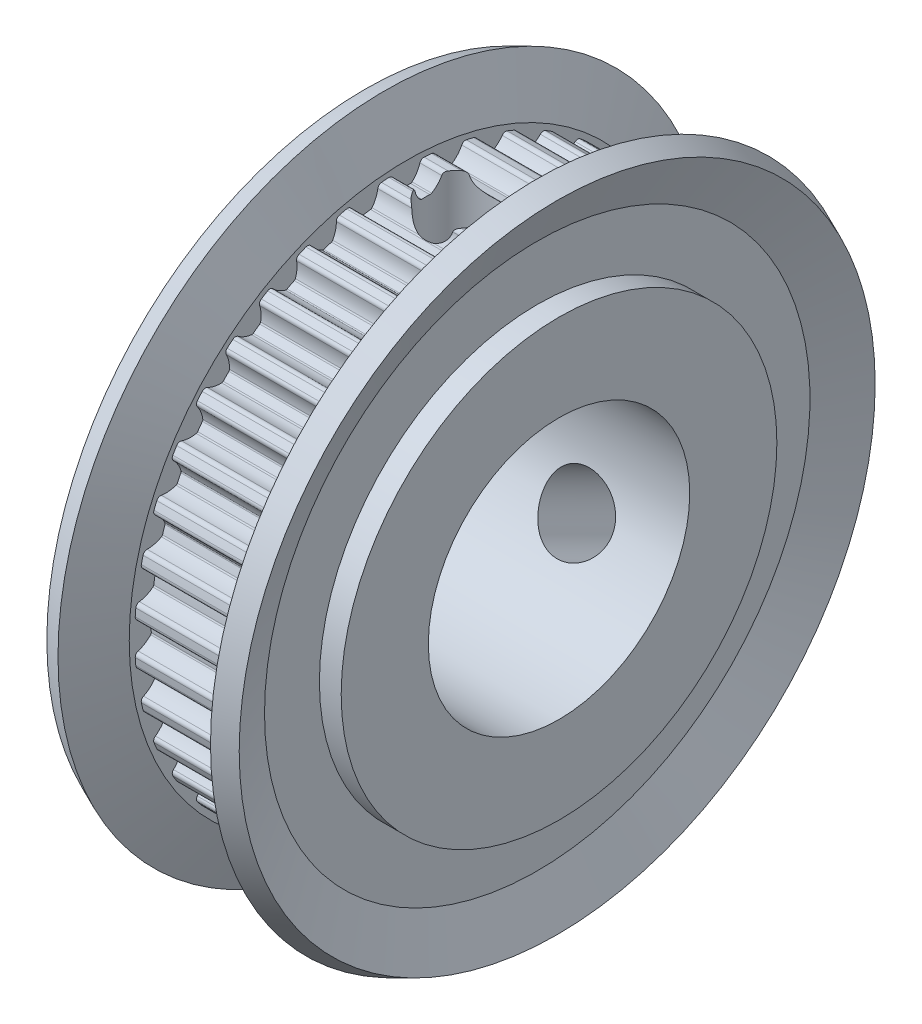
SolidWorks part; units mm, degrees
ref_plane "Front Plane" through (0, 0, 0) normal (0, 0, 1) x (1, 0, 0)
ref_plane "Top Plane" through (0, 0, 0) normal (0, 1, 0) x (1, 0, 0)
ref_plane "Right Plane" through (0, 0, 0) normal (1, 0, 0) x (0, 0, -1)
ref_plane "Plane1" through (0, 0, 0) normal (0, 0, 1) x (1, 0, 0)
sketch "Sketch1" plane through (0, 0, 0) normal (0, 0, 1) x (1, 0, 0)
  line L0 (0, 10) -> (0, 6)
  line L1 (0, 6) -> (17, 6)
  line L2 (17, 6) -> (17, 7)
  line L3 (17, 7) -> (9, 7)
  line L4 (9, 7) -> (9, 10)
  line L5 (9, 10) -> (8, 10)
  line L6 (8, 10) -> (8, 12.5195)
  line L7 (8, 12.5195) -> (8.9151, 14.5969)
  line L8 (8.9151, 14.5969) -> (8, 15)
  line L9 (8, 15) -> (7, 12.73)
  line L10 (7, 12.73) -> (7, 12.48)
  line L11 (7, 12.48) -> (2, 12.48)
  line L12 (2, 12.48) -> (2, 12.73)
  line L13 (2, 12.73) -> (1, 15)
  line L14 (1, 15) -> (0.0849, 14.5969)
  line L15 (0.0849, 14.5969) -> (1, 12.5195)
  line L16 (1, 12.5195) -> (1, 10)
  line L17 (1, 10) -> (0, 10)
  line L18 (17, 0) -> (0, 0) construction
revolve "Revolve1" add sketch "Sketch1" angle 360 about L18
ref_plane "Plane2" through (0, 0, 0) normal (0, 0, 1) x (1, 0, 0)
sketch "Sketch2" plane through (0, 0, 0) normal (0, 0, 1) x (1, 0, 0)
  line L0 (9, 0) -> (9, 15)
  line L1 (9, 15) -> (18, 15)
  line L2 (18, 15) -> (18, 0)
  line L3 (18, 0) -> (9, 0)
  line L4 (18, 0) -> (9, 0) construction
revolve "Cut-Revolve1" cut sketch "Sketch2" angle 360 about L4
ref_plane "Plane3" through (2, 0, 0) normal (1, 0, 0) x (0, 0, -1)
sketch "Sketch3" plane through (2, 0, 0) normal (1, 0, 0) x (0, 0, -1)
  line L0 (0.8092, 12.4537) -> (0.8092, 16.64)
  line L1 (0.8092, 16.64) -> (-0.8092, 16.64)
  line L2 (-0.8092, 16.64) -> (-0.8092, 12.4537)
  arc A0 (-0.8092, 12.4537) -> (-0.6154, 12.3205) centre (-0.7969, 12.2641) cw
  arc A1 (-0.6154, 12.3205) -> (-0.2549, 11.7455) centre (0.65, 12.7134) ccw
  arc A2 (-0.2549, 11.7455) -> (-0.185, 11.7185) centre (-0.1866, 11.8185) ccw
  arc A3 (-0.185, 11.7185) -> (0.185, 11.7185) centre (0, 0) cw
  arc A4 (0.185, 11.7185) -> (0.2549, 11.7455) centre (0.1866, 11.8185) ccw
  arc A5 (0.2549, 11.7455) -> (0.6154, 12.3205) centre (-0.65, 12.7134) ccw
  arc A6 (0.6154, 12.3205) -> (0.8092, 12.4537) centre (0.7969, 12.2641) cw
extrude "Cut-Extrude1" cut sketch "Sketch3" along normal blind 5
ref_plane "Plane4" through (2, 0, 0) normal (1, 0, 0) x (0, 0, -1)
sketch "Sketch4" plane through (2, 0, 0) normal (1, 0, 0) x (0, 0, -1)
  line L0 (-1.149, 12.427) -> (-1.8039, 16.5617)
  line L1 (-1.8039, 16.5617) -> (-3.4023, 16.3086)
  line L2 (-3.4023, 16.3086) -> (-2.7474, 12.1738)
  arc A0 (-2.7474, 12.1738) -> (-2.5352, 12.0725) centre (-2.7056, 11.9885) cw
  arc A1 (-2.5352, 12.0725) -> (-2.0891, 11.561) centre (-1.3468, 12.6586) ccw
  arc A2 (-2.0891, 11.561) -> (-2.0159, 11.5453) centre (-2.0331, 11.6438) ccw
  arc A3 (-2.0159, 11.5453) -> (-1.6505, 11.6032) centre (0, 0) cw
  arc A4 (-1.6505, 11.6032) -> (-1.5857, 11.6407) centre (-1.6646, 11.7022) ccw
  arc A5 (-1.5857, 11.6407) -> (-1.3195, 12.2651) centre (-2.6308, 12.4552) ccw
  arc A6 (-1.3195, 12.2651) -> (-1.149, 12.427) centre (-1.1315, 12.2378) cw
extrude "Cut-Extrude2" cut sketch "Sketch4" along normal blind 5
ref_plane "Plane5" through (2, 0, 0) normal (1, 0, 0) x (0, 0, -1)
sketch "Sketch5" plane through (2, 0, 0) normal (1, 0, 0) x (0, 0, -1)
  line L0 (-3.0788, 12.0943) -> (-4.3725, 16.0756)
  line L1 (-4.3725, 16.0756) -> (-5.9116, 15.5755)
  line L2 (-5.9116, 15.5755) -> (-4.618, 11.5942)
  arc A0 (-4.618, 11.5942) -> (-4.3925, 11.5273) centre (-4.5477, 11.4176) cw
  arc A1 (-4.3925, 11.5273) -> (-3.8719, 11.0919) centre (-3.3105, 12.292) ccw
  arc A2 (-3.8719, 11.0919) -> (-3.7972, 11.0878) centre (-3.8296, 11.1824) ccw
  arc A3 (-3.7972, 11.0878) -> (-3.4453, 11.2022) centre (0, 0) cw
  arc A4 (-3.4453, 11.2022) -> (-3.3872, 11.2494) centre (-3.4747, 11.2977) ccw
  arc A5 (-3.3872, 11.2494) -> (-3.222, 11.9076) centre (-4.5468, 11.8903) ccw
  arc A6 (-3.222, 11.9076) -> (-3.0788, 12.0943) centre (-3.032, 11.9101) cw
extrude "Cut-Extrude3" cut sketch "Sketch5" along normal blind 5
ref_plane "Plane6" through (2, 0, 0) normal (1, 0, 0) x (0, 0, -1)
sketch "Sketch6" plane through (2, 0, 0) normal (1, 0, 0) x (0, 0, -1)
  line L0 (-4.9329, 11.4637) -> (-6.8334, 15.1937)
  line L1 (-6.8334, 15.1937) -> (-8.2754, 14.459)
  line L2 (-8.2754, 14.459) -> (-6.3749, 10.729)
  arc A0 (-6.3749, 10.729) -> (-6.1417, 10.6982) centre (-6.2778, 10.5657) cw
  arc A1 (-6.1417, 10.6982) -> (-5.5594, 10.3496) centre (-5.1926, 11.6228) ccw
  arc A2 (-5.5594, 10.3496) -> (-5.4849, 10.3573) centre (-5.5317, 10.4457) ccw
  arc A3 (-5.4849, 10.3573) -> (-5.1553, 10.5253) centre (0, 0) cw
  arc A4 (-5.1553, 10.5253) -> (-5.1053, 10.581) centre (-5.1993, 10.6151) ccw
  arc A5 (-5.1053, 10.581) -> (-5.0451, 11.257) centre (-6.3509, 11.0326) ccw
  arc A6 (-5.0451, 11.257) -> (-4.9329, 11.4637) centre (-4.8578, 11.2892) cw
extrude "Cut-Extrude4" cut sketch "Sketch6" along normal blind 5
ref_plane "Plane7" through (2, 0, 0) normal (1, 0, 0) x (0, 0, -1)
sketch "Sketch7" plane through (2, 0, 0) normal (1, 0, 0) x (0, 0, -1)
  line L0 (-6.6655, 10.5509) -> (-9.1261, 13.9377)
  line L1 (-9.1261, 13.9377) -> (-10.4354, 12.9864)
  line L2 (-10.4354, 12.9864) -> (-7.9748, 9.5997)
  arc A0 (-7.9748, 9.5997) -> (-7.7397, 9.6058) centre (-7.8534, 9.4535) cw
  arc A1 (-7.7397, 9.6058) -> (-7.11, 9.3525) centre (-6.9469, 10.6674) ccw
  arc A2 (-7.11, 9.3525) -> (-7.0376, 9.3718) centre (-7.0977, 9.4517) ccw
  arc A3 (-7.0376, 9.3718) -> (-6.7383, 9.5892) centre (0, 0) cw
  arc A4 (-6.7383, 9.5892) -> (-6.6976, 9.6521) centre (-6.7958, 9.671) ccw
  arc A5 (-6.6976, 9.6521) -> (-6.7439, 10.3292) centre (-7.9986, 9.9033) ccw
  arc A6 (-6.7439, 10.3292) -> (-6.6655, 10.5509) centre (-6.564, 10.3903) cw
extrude "Cut-Extrude5" cut sketch "Sketch7" along normal blind 5
ref_plane "Plane8" through (2, 0, 0) normal (1, 0, 0) x (0, 0, -1)
sketch "Sketch8" plane through (2, 0, 0) normal (1, 0, 0) x (0, 0, -1)
  line L0 (-8.2339, 9.3783) -> (-11.1941, 12.3384)
  line L1 (-11.1941, 12.3384) -> (-12.3384, 11.1941)
  line L2 (-12.3384, 11.1941) -> (-9.3783, 8.2339)
  arc A0 (-9.3783, 8.2339) -> (-9.1471, 8.2767) centre (-9.2355, 8.1086) cw
  arc A1 (-9.1471, 8.2767) -> (-8.4855, 8.1251) centre (-8.5301, 9.4493) ccw
  arc A2 (-8.4855, 8.1251) -> (-8.4171, 8.1555) centre (-8.4889, 8.225) ccw
  arc A3 (-8.4171, 8.1555) -> (-8.1555, 8.4171) centre (0, 0) cw
  arc A4 (-8.1555, 8.4171) -> (-8.1251, 8.4855) centre (-8.225, 8.4889) ccw
  arc A5 (-8.1251, 8.4855) -> (-8.2767, 9.1471) centre (-9.4493, 8.5301) ccw
  arc A6 (-8.2767, 9.1471) -> (-8.2339, 9.3783) centre (-8.1086, 9.2355) cw
extrude "Cut-Extrude6" cut sketch "Sketch8" along normal blind 5
ref_plane "Plane9" through (2, 0, 0) normal (1, 0, 0) x (0, 0, -1)
sketch "Sketch9" plane through (2, 0, 0) normal (1, 0, 0) x (0, 0, -1)
  line L0 (-9.5997, 7.9748) -> (-12.9864, 10.4354)
  line L1 (-12.9864, 10.4354) -> (-13.9377, 9.1261)
  line L2 (-13.9377, 9.1261) -> (-10.5509, 6.6655)
  arc A0 (-10.5509, 6.6655) -> (-10.3292, 6.7439) centre (-10.3903, 6.564) cw
  arc A1 (-10.3292, 6.7439) -> (-9.6521, 6.6976) centre (-9.9033, 7.9986) ccw
  arc A2 (-9.6521, 6.6976) -> (-9.5892, 6.7383) centre (-9.671, 6.7958) ccw
  arc A3 (-9.5892, 6.7383) -> (-9.3718, 7.0376) centre (0, 0) cw
  arc A4 (-9.3718, 7.0376) -> (-9.3525, 7.11) centre (-9.4517, 7.0977) ccw
  arc A5 (-9.3525, 7.11) -> (-9.6058, 7.7397) centre (-10.6674, 6.9469) ccw
  arc A6 (-9.6058, 7.7397) -> (-9.5997, 7.9748) centre (-9.4535, 7.8534) cw
extrude "Cut-Extrude7" cut sketch "Sketch9" along normal blind 5
ref_plane "Plane10" through (2, 0, 0) normal (1, 0, 0) x (0, 0, -1)
sketch "Sketch10" plane through (2, 0, 0) normal (1, 0, 0) x (0, 0, -1)
  line L0 (-10.729, 6.3749) -> (-14.459, 8.2754)
  line L1 (-14.459, 8.2754) -> (-15.1937, 6.8334)
  line L2 (-15.1937, 6.8334) -> (-11.4637, 4.9329)
  arc A0 (-11.4637, 4.9329) -> (-11.257, 5.0451) centre (-11.2892, 4.8578) cw
  arc A1 (-11.257, 5.0451) -> (-10.581, 5.1053) centre (-11.0326, 6.3509) ccw
  arc A2 (-10.581, 5.1053) -> (-10.5253, 5.1553) centre (-10.6151, 5.1993) ccw
  arc A3 (-10.5253, 5.1553) -> (-10.3573, 5.4849) centre (0, 0) cw
  arc A4 (-10.3573, 5.4849) -> (-10.3496, 5.5594) centre (-10.4457, 5.5317) ccw
  arc A5 (-10.3496, 5.5594) -> (-10.6982, 6.1417) centre (-11.6228, 5.1926) ccw
  arc A6 (-10.6982, 6.1417) -> (-10.729, 6.3749) centre (-10.5657, 6.2778) cw
extrude "Cut-Extrude8" cut sketch "Sketch10" along normal blind 5
ref_plane "Plane11" through (2, 0, 0) normal (1, 0, 0) x (0, 0, -1)
sketch "Sketch11" plane through (2, 0, 0) normal (1, 0, 0) x (0, 0, -1)
  line L0 (-11.5942, 4.618) -> (-15.5755, 5.9116)
  line L1 (-15.5755, 5.9116) -> (-16.0756, 4.3725)
  line L2 (-16.0756, 4.3725) -> (-12.0943, 3.0788)
  arc A0 (-12.0943, 3.0788) -> (-11.9076, 3.222) centre (-11.9101, 3.032) cw
  arc A1 (-11.9076, 3.222) -> (-11.2494, 3.3872) centre (-11.8903, 4.5468) ccw
  arc A2 (-11.2494, 3.3872) -> (-11.2022, 3.4453) centre (-11.2977, 3.4747) ccw
  arc A3 (-11.2022, 3.4453) -> (-11.0878, 3.7972) centre (0, 0) cw
  arc A4 (-11.0878, 3.7972) -> (-11.0919, 3.8719) centre (-11.1824, 3.8296) ccw
  arc A5 (-11.0919, 3.8719) -> (-11.5273, 4.3925) centre (-12.292, 3.3105) ccw
  arc A6 (-11.5273, 4.3925) -> (-11.5942, 4.618) centre (-11.4176, 4.5477) cw
extrude "Cut-Extrude9" cut sketch "Sketch11" along normal blind 5
ref_plane "Plane12" through (2, 0, 0) normal (1, 0, 0) x (0, 0, -1)
sketch "Sketch12" plane through (2, 0, 0) normal (1, 0, 0) x (0, 0, -1)
  line L0 (-12.1738, 2.7474) -> (-16.3086, 3.4023)
  line L1 (-16.3086, 3.4023) -> (-16.5617, 1.8039)
  line L2 (-16.5617, 1.8039) -> (-12.427, 1.149)
  arc A0 (-12.427, 1.149) -> (-12.2651, 1.3195) centre (-12.2378, 1.1315) cw
  arc A1 (-12.2651, 1.3195) -> (-11.6407, 1.5857) centre (-12.4552, 2.6308) ccw
  arc A2 (-11.6407, 1.5857) -> (-11.6032, 1.6505) centre (-11.7022, 1.6646) ccw
  arc A3 (-11.6032, 1.6505) -> (-11.5453, 2.0159) centre (0, 0) cw
  arc A4 (-11.5453, 2.0159) -> (-11.561, 2.0891) centre (-11.6438, 2.0331) ccw
  arc A5 (-11.561, 2.0891) -> (-12.0725, 2.5352) centre (-12.6586, 1.3468) ccw
  arc A6 (-12.0725, 2.5352) -> (-12.1738, 2.7474) centre (-11.9885, 2.7056) cw
extrude "Cut-Extrude10" cut sketch "Sketch12" along normal blind 5
ref_plane "Plane13" through (2, 0, 0) normal (1, 0, 0) x (0, 0, -1)
sketch "Sketch13" plane through (2, 0, 0) normal (1, 0, 0) x (0, 0, -1)
  line L0 (-12.4537, 0.8092) -> (-16.64, 0.8092)
  line L1 (-16.64, 0.8092) -> (-16.64, -0.8092)
  line L2 (-16.64, -0.8092) -> (-12.4537, -0.8092)
  arc A0 (-12.4537, -0.8092) -> (-12.3205, -0.6154) centre (-12.2641, -0.7969) cw
  arc A1 (-12.3205, -0.6154) -> (-11.7455, -0.2549) centre (-12.7134, 0.65) ccw
  arc A2 (-11.7455, -0.2549) -> (-11.7185, -0.185) centre (-11.8185, -0.1866) ccw
  arc A3 (-11.7185, -0.185) -> (-11.7185, 0.185) centre (0, 0) cw
  arc A4 (-11.7185, 0.185) -> (-11.7455, 0.2549) centre (-11.8185, 0.1866) ccw
  arc A5 (-11.7455, 0.2549) -> (-12.3205, 0.6154) centre (-12.7134, -0.65) ccw
  arc A6 (-12.3205, 0.6154) -> (-12.4537, 0.8092) centre (-12.2641, 0.7969) cw
extrude "Cut-Extrude11" cut sketch "Sketch13" along normal blind 5
ref_plane "Plane14" through (2, 0, 0) normal (1, 0, 0) x (0, 0, -1)
sketch "Sketch14" plane through (2, 0, 0) normal (1, 0, 0) x (0, 0, -1)
  line L0 (-12.427, -1.149) -> (-16.5617, -1.8039)
  line L1 (-16.5617, -1.8039) -> (-16.3086, -3.4023)
  line L2 (-16.3086, -3.4023) -> (-12.1738, -2.7474)
  arc A0 (-12.1738, -2.7474) -> (-12.0725, -2.5352) centre (-11.9885, -2.7056) cw
  arc A1 (-12.0725, -2.5352) -> (-11.561, -2.0891) centre (-12.6586, -1.3468) ccw
  arc A2 (-11.561, -2.0891) -> (-11.5453, -2.0159) centre (-11.6438, -2.0331) ccw
  arc A3 (-11.5453, -2.0159) -> (-11.6032, -1.6505) centre (0, 0) cw
  arc A4 (-11.6032, -1.6505) -> (-11.6407, -1.5857) centre (-11.7022, -1.6646) ccw
  arc A5 (-11.6407, -1.5857) -> (-12.2651, -1.3195) centre (-12.4552, -2.6308) ccw
  arc A6 (-12.2651, -1.3195) -> (-12.427, -1.149) centre (-12.2378, -1.1315) cw
extrude "Cut-Extrude12" cut sketch "Sketch14" along normal blind 5
ref_plane "Plane15" through (2, 0, 0) normal (1, 0, 0) x (0, 0, -1)
sketch "Sketch15" plane through (2, 0, 0) normal (1, 0, 0) x (0, 0, -1)
  line L0 (-12.0943, -3.0788) -> (-16.0756, -4.3725)
  line L1 (-16.0756, -4.3725) -> (-15.5755, -5.9116)
  line L2 (-15.5755, -5.9116) -> (-11.5942, -4.618)
  arc A0 (-11.5942, -4.618) -> (-11.5273, -4.3925) centre (-11.4176, -4.5477) cw
  arc A1 (-11.5273, -4.3925) -> (-11.0919, -3.8719) centre (-12.292, -3.3105) ccw
  arc A2 (-11.0919, -3.8719) -> (-11.0878, -3.7972) centre (-11.1824, -3.8296) ccw
  arc A3 (-11.0878, -3.7972) -> (-11.2022, -3.4453) centre (0, 0) cw
  arc A4 (-11.2022, -3.4453) -> (-11.2494, -3.3872) centre (-11.2977, -3.4747) ccw
  arc A5 (-11.2494, -3.3872) -> (-11.9076, -3.222) centre (-11.8903, -4.5468) ccw
  arc A6 (-11.9076, -3.222) -> (-12.0943, -3.0788) centre (-11.9101, -3.032) cw
extrude "Cut-Extrude13" cut sketch "Sketch15" along normal blind 5
ref_plane "Plane16" through (2, 0, 0) normal (1, 0, 0) x (0, 0, -1)
sketch "Sketch16" plane through (2, 0, 0) normal (1, 0, 0) x (0, 0, -1)
  line L0 (-11.4637, -4.9329) -> (-15.1937, -6.8334)
  line L1 (-15.1937, -6.8334) -> (-14.459, -8.2754)
  line L2 (-14.459, -8.2754) -> (-10.729, -6.3749)
  arc A0 (-10.729, -6.3749) -> (-10.6982, -6.1417) centre (-10.5657, -6.2778) cw
  arc A1 (-10.6982, -6.1417) -> (-10.3496, -5.5594) centre (-11.6228, -5.1926) ccw
  arc A2 (-10.3496, -5.5594) -> (-10.3573, -5.4849) centre (-10.4457, -5.5317) ccw
  arc A3 (-10.3573, -5.4849) -> (-10.5253, -5.1553) centre (0, 0) cw
  arc A4 (-10.5253, -5.1553) -> (-10.581, -5.1053) centre (-10.6151, -5.1993) ccw
  arc A5 (-10.581, -5.1053) -> (-11.257, -5.0451) centre (-11.0326, -6.3509) ccw
  arc A6 (-11.257, -5.0451) -> (-11.4637, -4.9329) centre (-11.2892, -4.8578) cw
extrude "Cut-Extrude14" cut sketch "Sketch16" along normal blind 5
ref_plane "Plane17" through (2, 0, 0) normal (1, 0, 0) x (0, 0, -1)
sketch "Sketch17" plane through (2, 0, 0) normal (1, 0, 0) x (0, 0, -1)
  line L0 (-10.5509, -6.6655) -> (-13.9377, -9.1261)
  line L1 (-13.9377, -9.1261) -> (-12.9864, -10.4354)
  line L2 (-12.9864, -10.4354) -> (-9.5997, -7.9748)
  arc A0 (-9.5997, -7.9748) -> (-9.6058, -7.7397) centre (-9.4535, -7.8534) cw
  arc A1 (-9.6058, -7.7397) -> (-9.3525, -7.11) centre (-10.6674, -6.9469) ccw
  arc A2 (-9.3525, -7.11) -> (-9.3718, -7.0376) centre (-9.4517, -7.0977) ccw
  arc A3 (-9.3718, -7.0376) -> (-9.5892, -6.7383) centre (0, 0) cw
  arc A4 (-9.5892, -6.7383) -> (-9.6521, -6.6976) centre (-9.671, -6.7958) ccw
  arc A5 (-9.6521, -6.6976) -> (-10.3292, -6.7439) centre (-9.9033, -7.9986) ccw
  arc A6 (-10.3292, -6.7439) -> (-10.5509, -6.6655) centre (-10.3903, -6.564) cw
extrude "Cut-Extrude15" cut sketch "Sketch17" along normal blind 5
ref_plane "Plane18" through (2, 0, 0) normal (1, 0, 0) x (0, 0, -1)
sketch "Sketch18" plane through (2, 0, 0) normal (1, 0, 0) x (0, 0, -1)
  line L0 (-9.3783, -8.2339) -> (-12.3384, -11.1941)
  line L1 (-12.3384, -11.1941) -> (-11.1941, -12.3384)
  line L2 (-11.1941, -12.3384) -> (-8.2339, -9.3783)
  arc A0 (-8.2339, -9.3783) -> (-8.2767, -9.1471) centre (-8.1086, -9.2355) cw
  arc A1 (-8.2767, -9.1471) -> (-8.1251, -8.4855) centre (-9.4493, -8.5301) ccw
  arc A2 (-8.1251, -8.4855) -> (-8.1555, -8.4171) centre (-8.225, -8.4889) ccw
  arc A3 (-8.1555, -8.4171) -> (-8.4171, -8.1555) centre (0, 0) cw
  arc A4 (-8.4171, -8.1555) -> (-8.4855, -8.1251) centre (-8.4889, -8.225) ccw
  arc A5 (-8.4855, -8.1251) -> (-9.1471, -8.2767) centre (-8.5301, -9.4493) ccw
  arc A6 (-9.1471, -8.2767) -> (-9.3783, -8.2339) centre (-9.2355, -8.1086) cw
extrude "Cut-Extrude16" cut sketch "Sketch18" along normal blind 5
ref_plane "Plane19" through (2, 0, 0) normal (1, 0, 0) x (0, 0, -1)
sketch "Sketch19" plane through (2, 0, 0) normal (1, 0, 0) x (0, 0, -1)
  line L0 (-7.9748, -9.5997) -> (-10.4354, -12.9864)
  line L1 (-10.4354, -12.9864) -> (-9.1261, -13.9377)
  line L2 (-9.1261, -13.9377) -> (-6.6655, -10.5509)
  arc A0 (-6.6655, -10.5509) -> (-6.7439, -10.3292) centre (-6.564, -10.3903) cw
  arc A1 (-6.7439, -10.3292) -> (-6.6976, -9.6521) centre (-7.9986, -9.9033) ccw
  arc A2 (-6.6976, -9.6521) -> (-6.7383, -9.5892) centre (-6.7958, -9.671) ccw
  arc A3 (-6.7383, -9.5892) -> (-7.0376, -9.3718) centre (0, 0) cw
  arc A4 (-7.0376, -9.3718) -> (-7.11, -9.3525) centre (-7.0977, -9.4517) ccw
  arc A5 (-7.11, -9.3525) -> (-7.7397, -9.6058) centre (-6.9469, -10.6674) ccw
  arc A6 (-7.7397, -9.6058) -> (-7.9748, -9.5997) centre (-7.8534, -9.4535) cw
extrude "Cut-Extrude17" cut sketch "Sketch19" along normal blind 5
ref_plane "Plane20" through (2, 0, 0) normal (1, 0, 0) x (0, 0, -1)
sketch "Sketch20" plane through (2, 0, 0) normal (1, 0, 0) x (0, 0, -1)
  line L0 (-6.3749, -10.729) -> (-8.2754, -14.459)
  line L1 (-8.2754, -14.459) -> (-6.8334, -15.1937)
  line L2 (-6.8334, -15.1937) -> (-4.9329, -11.4637)
  arc A0 (-4.9329, -11.4637) -> (-5.0451, -11.257) centre (-4.8578, -11.2892) cw
  arc A1 (-5.0451, -11.257) -> (-5.1053, -10.581) centre (-6.3509, -11.0326) ccw
  arc A2 (-5.1053, -10.581) -> (-5.1553, -10.5253) centre (-5.1993, -10.6151) ccw
  arc A3 (-5.1553, -10.5253) -> (-5.4849, -10.3573) centre (0, 0) cw
  arc A4 (-5.4849, -10.3573) -> (-5.5594, -10.3496) centre (-5.5317, -10.4457) ccw
  arc A5 (-5.5594, -10.3496) -> (-6.1417, -10.6982) centre (-5.1926, -11.6228) ccw
  arc A6 (-6.1417, -10.6982) -> (-6.3749, -10.729) centre (-6.2778, -10.5657) cw
extrude "Cut-Extrude18" cut sketch "Sketch20" along normal blind 5
ref_plane "Plane21" through (2, 0, 0) normal (1, 0, 0) x (0, 0, -1)
sketch "Sketch21" plane through (2, 0, 0) normal (1, 0, 0) x (0, 0, -1)
  line L0 (-4.618, -11.5942) -> (-5.9116, -15.5755)
  line L1 (-5.9116, -15.5755) -> (-4.3725, -16.0756)
  line L2 (-4.3725, -16.0756) -> (-3.0788, -12.0943)
  arc A0 (-3.0788, -12.0943) -> (-3.222, -11.9076) centre (-3.032, -11.9101) cw
  arc A1 (-3.222, -11.9076) -> (-3.3872, -11.2494) centre (-4.5468, -11.8903) ccw
  arc A2 (-3.3872, -11.2494) -> (-3.4453, -11.2022) centre (-3.4747, -11.2977) ccw
  arc A3 (-3.4453, -11.2022) -> (-3.7972, -11.0878) centre (0, 0) cw
  arc A4 (-3.7972, -11.0878) -> (-3.8719, -11.0919) centre (-3.8296, -11.1824) ccw
  arc A5 (-3.8719, -11.0919) -> (-4.3925, -11.5273) centre (-3.3105, -12.292) ccw
  arc A6 (-4.3925, -11.5273) -> (-4.618, -11.5942) centre (-4.5477, -11.4176) cw
extrude "Cut-Extrude19" cut sketch "Sketch21" along normal blind 5
ref_plane "Plane22" through (2, 0, 0) normal (1, 0, 0) x (0, 0, -1)
sketch "Sketch22" plane through (2, 0, 0) normal (1, 0, 0) x (0, 0, -1)
  line L0 (-2.7474, -12.1738) -> (-3.4023, -16.3086)
  line L1 (-3.4023, -16.3086) -> (-1.8039, -16.5617)
  line L2 (-1.8039, -16.5617) -> (-1.149, -12.427)
  arc A0 (-1.149, -12.427) -> (-1.3195, -12.2651) centre (-1.1315, -12.2378) cw
  arc A1 (-1.3195, -12.2651) -> (-1.5857, -11.6407) centre (-2.6308, -12.4552) ccw
  arc A2 (-1.5857, -11.6407) -> (-1.6505, -11.6032) centre (-1.6646, -11.7022) ccw
  arc A3 (-1.6505, -11.6032) -> (-2.0159, -11.5453) centre (0, 0) cw
  arc A4 (-2.0159, -11.5453) -> (-2.0891, -11.561) centre (-2.0331, -11.6438) ccw
  arc A5 (-2.0891, -11.561) -> (-2.5352, -12.0725) centre (-1.3468, -12.6586) ccw
  arc A6 (-2.5352, -12.0725) -> (-2.7474, -12.1738) centre (-2.7056, -11.9885) cw
extrude "Cut-Extrude20" cut sketch "Sketch22" along normal blind 5
ref_plane "Plane23" through (2, 0, 0) normal (1, 0, 0) x (0, 0, -1)
sketch "Sketch23" plane through (2, 0, 0) normal (1, 0, 0) x (0, 0, -1)
  line L0 (-0.8092, -12.4537) -> (-0.8092, -16.64)
  line L1 (-0.8092, -16.64) -> (0.8092, -16.64)
  line L2 (0.8092, -16.64) -> (0.8092, -12.4537)
  arc A0 (0.8092, -12.4537) -> (0.6154, -12.3205) centre (0.7969, -12.2641) cw
  arc A1 (0.6154, -12.3205) -> (0.2549, -11.7455) centre (-0.65, -12.7134) ccw
  arc A2 (0.2549, -11.7455) -> (0.185, -11.7185) centre (0.1866, -11.8185) ccw
  arc A3 (0.185, -11.7185) -> (-0.185, -11.7185) centre (0, 0) cw
  arc A4 (-0.185, -11.7185) -> (-0.2549, -11.7455) centre (-0.1866, -11.8185) ccw
  arc A5 (-0.2549, -11.7455) -> (-0.6154, -12.3205) centre (0.65, -12.7134) ccw
  arc A6 (-0.6154, -12.3205) -> (-0.8092, -12.4537) centre (-0.7969, -12.2641) cw
extrude "Cut-Extrude21" cut sketch "Sketch23" along normal blind 5
ref_plane "Plane24" through (2, 0, 0) normal (1, 0, 0) x (0, 0, -1)
sketch "Sketch24" plane through (2, 0, 0) normal (1, 0, 0) x (0, 0, -1)
  line L0 (1.149, -12.427) -> (1.8039, -16.5617)
  line L1 (1.8039, -16.5617) -> (3.4023, -16.3086)
  line L2 (3.4023, -16.3086) -> (2.7474, -12.1738)
  arc A0 (2.7474, -12.1738) -> (2.5352, -12.0725) centre (2.7056, -11.9885) cw
  arc A1 (2.5352, -12.0725) -> (2.0891, -11.561) centre (1.3468, -12.6586) ccw
  arc A2 (2.0891, -11.561) -> (2.0159, -11.5453) centre (2.0331, -11.6438) ccw
  arc A3 (2.0159, -11.5453) -> (1.6505, -11.6032) centre (0, 0) cw
  arc A4 (1.6505, -11.6032) -> (1.5857, -11.6407) centre (1.6646, -11.7022) ccw
  arc A5 (1.5857, -11.6407) -> (1.3195, -12.2651) centre (2.6308, -12.4552) ccw
  arc A6 (1.3195, -12.2651) -> (1.149, -12.427) centre (1.1315, -12.2378) cw
extrude "Cut-Extrude22" cut sketch "Sketch24" along normal blind 5
ref_plane "Plane25" through (2, 0, 0) normal (1, 0, 0) x (0, 0, -1)
sketch "Sketch25" plane through (2, 0, 0) normal (1, 0, 0) x (0, 0, -1)
  line L0 (3.0788, -12.0943) -> (4.3725, -16.0756)
  line L1 (4.3725, -16.0756) -> (5.9116, -15.5755)
  line L2 (5.9116, -15.5755) -> (4.618, -11.5942)
  arc A0 (4.618, -11.5942) -> (4.3925, -11.5273) centre (4.5477, -11.4176) cw
  arc A1 (4.3925, -11.5273) -> (3.8719, -11.0919) centre (3.3105, -12.292) ccw
  arc A2 (3.8719, -11.0919) -> (3.7972, -11.0878) centre (3.8296, -11.1824) ccw
  arc A3 (3.7972, -11.0878) -> (3.4453, -11.2022) centre (0, 0) cw
  arc A4 (3.4453, -11.2022) -> (3.3872, -11.2494) centre (3.4747, -11.2977) ccw
  arc A5 (3.3872, -11.2494) -> (3.222, -11.9076) centre (4.5468, -11.8903) ccw
  arc A6 (3.222, -11.9076) -> (3.0788, -12.0943) centre (3.032, -11.9101) cw
extrude "Cut-Extrude23" cut sketch "Sketch25" along normal blind 5
ref_plane "Plane26" through (2, 0, 0) normal (1, 0, 0) x (0, 0, -1)
sketch "Sketch26" plane through (2, 0, 0) normal (1, 0, 0) x (0, 0, -1)
  line L0 (4.9329, -11.4637) -> (6.8334, -15.1937)
  line L1 (6.8334, -15.1937) -> (8.2754, -14.459)
  line L2 (8.2754, -14.459) -> (6.3749, -10.729)
  arc A0 (6.3749, -10.729) -> (6.1417, -10.6982) centre (6.2778, -10.5657) cw
  arc A1 (6.1417, -10.6982) -> (5.5594, -10.3496) centre (5.1926, -11.6228) ccw
  arc A2 (5.5594, -10.3496) -> (5.4849, -10.3573) centre (5.5317, -10.4457) ccw
  arc A3 (5.4849, -10.3573) -> (5.1553, -10.5253) centre (0, 0) cw
  arc A4 (5.1553, -10.5253) -> (5.1053, -10.581) centre (5.1993, -10.6151) ccw
  arc A5 (5.1053, -10.581) -> (5.0451, -11.257) centre (6.3509, -11.0326) ccw
  arc A6 (5.0451, -11.257) -> (4.9329, -11.4637) centre (4.8578, -11.2892) cw
extrude "Cut-Extrude24" cut sketch "Sketch26" along normal blind 5
ref_plane "Plane27" through (2, 0, 0) normal (1, 0, 0) x (0, 0, -1)
sketch "Sketch27" plane through (2, 0, 0) normal (1, 0, 0) x (0, 0, -1)
  line L0 (6.6655, -10.5509) -> (9.1261, -13.9377)
  line L1 (9.1261, -13.9377) -> (10.4354, -12.9864)
  line L2 (10.4354, -12.9864) -> (7.9748, -9.5997)
  arc A0 (7.9748, -9.5997) -> (7.7397, -9.6058) centre (7.8534, -9.4535) cw
  arc A1 (7.7397, -9.6058) -> (7.11, -9.3525) centre (6.9469, -10.6674) ccw
  arc A2 (7.11, -9.3525) -> (7.0376, -9.3718) centre (7.0977, -9.4517) ccw
  arc A3 (7.0376, -9.3718) -> (6.7383, -9.5892) centre (0, 0) cw
  arc A4 (6.7383, -9.5892) -> (6.6976, -9.6521) centre (6.7958, -9.671) ccw
  arc A5 (6.6976, -9.6521) -> (6.7439, -10.3292) centre (7.9986, -9.9033) ccw
  arc A6 (6.7439, -10.3292) -> (6.6655, -10.5509) centre (6.564, -10.3903) cw
extrude "Cut-Extrude25" cut sketch "Sketch27" along normal blind 5
ref_plane "Plane28" through (2, 0, 0) normal (1, 0, 0) x (0, 0, -1)
sketch "Sketch28" plane through (2, 0, 0) normal (1, 0, 0) x (0, 0, -1)
  line L0 (8.2339, -9.3783) -> (11.1941, -12.3384)
  line L1 (11.1941, -12.3384) -> (12.3384, -11.1941)
  line L2 (12.3384, -11.1941) -> (9.3783, -8.2339)
  arc A0 (9.3783, -8.2339) -> (9.1471, -8.2767) centre (9.2355, -8.1086) cw
  arc A1 (9.1471, -8.2767) -> (8.4855, -8.1251) centre (8.5301, -9.4493) ccw
  arc A2 (8.4855, -8.1251) -> (8.4171, -8.1555) centre (8.4889, -8.225) ccw
  arc A3 (8.4171, -8.1555) -> (8.1555, -8.4171) centre (0, 0) cw
  arc A4 (8.1555, -8.4171) -> (8.1251, -8.4855) centre (8.225, -8.4889) ccw
  arc A5 (8.1251, -8.4855) -> (8.2767, -9.1471) centre (9.4493, -8.5301) ccw
  arc A6 (8.2767, -9.1471) -> (8.2339, -9.3783) centre (8.1086, -9.2355) cw
extrude "Cut-Extrude26" cut sketch "Sketch28" along normal blind 5
ref_plane "Plane29" through (2, 0, 0) normal (1, 0, 0) x (0, 0, -1)
sketch "Sketch29" plane through (2, 0, 0) normal (1, 0, 0) x (0, 0, -1)
  line L0 (9.5997, -7.9748) -> (12.9864, -10.4354)
  line L1 (12.9864, -10.4354) -> (13.9377, -9.1261)
  line L2 (13.9377, -9.1261) -> (10.5509, -6.6655)
  arc A0 (10.5509, -6.6655) -> (10.3292, -6.7439) centre (10.3903, -6.564) cw
  arc A1 (10.3292, -6.7439) -> (9.6521, -6.6976) centre (9.9033, -7.9986) ccw
  arc A2 (9.6521, -6.6976) -> (9.5892, -6.7383) centre (9.671, -6.7958) ccw
  arc A3 (9.5892, -6.7383) -> (9.3718, -7.0376) centre (0, 0) cw
  arc A4 (9.3718, -7.0376) -> (9.3525, -7.11) centre (9.4517, -7.0977) ccw
  arc A5 (9.3525, -7.11) -> (9.6058, -7.7397) centre (10.6674, -6.9469) ccw
  arc A6 (9.6058, -7.7397) -> (9.5997, -7.9748) centre (9.4535, -7.8534) cw
extrude "Cut-Extrude27" cut sketch "Sketch29" along normal blind 5
ref_plane "Plane30" through (2, 0, 0) normal (1, 0, 0) x (0, 0, -1)
sketch "Sketch30" plane through (2, 0, 0) normal (1, 0, 0) x (0, 0, -1)
  line L0 (10.729, -6.3749) -> (14.459, -8.2754)
  line L1 (14.459, -8.2754) -> (15.1937, -6.8334)
  line L2 (15.1937, -6.8334) -> (11.4637, -4.9329)
  arc A0 (11.4637, -4.9329) -> (11.257, -5.0451) centre (11.2892, -4.8578) cw
  arc A1 (11.257, -5.0451) -> (10.581, -5.1053) centre (11.0326, -6.3509) ccw
  arc A2 (10.581, -5.1053) -> (10.5253, -5.1553) centre (10.6151, -5.1993) ccw
  arc A3 (10.5253, -5.1553) -> (10.3573, -5.4849) centre (0, 0) cw
  arc A4 (10.3573, -5.4849) -> (10.3496, -5.5594) centre (10.4457, -5.5317) ccw
  arc A5 (10.3496, -5.5594) -> (10.6982, -6.1417) centre (11.6228, -5.1926) ccw
  arc A6 (10.6982, -6.1417) -> (10.729, -6.3749) centre (10.5657, -6.2778) cw
extrude "Cut-Extrude28" cut sketch "Sketch30" along normal blind 5
ref_plane "Plane31" through (2, 0, 0) normal (1, 0, 0) x (0, 0, -1)
sketch "Sketch31" plane through (2, 0, 0) normal (1, 0, 0) x (0, 0, -1)
  line L0 (11.5942, -4.618) -> (15.5755, -5.9116)
  line L1 (15.5755, -5.9116) -> (16.0756, -4.3725)
  line L2 (16.0756, -4.3725) -> (12.0943, -3.0788)
  arc A0 (12.0943, -3.0788) -> (11.9076, -3.222) centre (11.9101, -3.032) cw
  arc A1 (11.9076, -3.222) -> (11.2494, -3.3872) centre (11.8903, -4.5468) ccw
  arc A2 (11.2494, -3.3872) -> (11.2022, -3.4453) centre (11.2977, -3.4747) ccw
  arc A3 (11.2022, -3.4453) -> (11.0878, -3.7972) centre (0, 0) cw
  arc A4 (11.0878, -3.7972) -> (11.0919, -3.8719) centre (11.1824, -3.8296) ccw
  arc A5 (11.0919, -3.8719) -> (11.5273, -4.3925) centre (12.292, -3.3105) ccw
  arc A6 (11.5273, -4.3925) -> (11.5942, -4.618) centre (11.4176, -4.5477) cw
extrude "Cut-Extrude29" cut sketch "Sketch31" along normal blind 5
ref_plane "Plane32" through (2, 0, 0) normal (1, 0, 0) x (0, 0, -1)
sketch "Sketch32" plane through (2, 0, 0) normal (1, 0, 0) x (0, 0, -1)
  line L0 (12.1738, -2.7474) -> (16.3086, -3.4023)
  line L1 (16.3086, -3.4023) -> (16.5617, -1.8039)
  line L2 (16.5617, -1.8039) -> (12.427, -1.149)
  arc A0 (12.427, -1.149) -> (12.2651, -1.3195) centre (12.2378, -1.1315) cw
  arc A1 (12.2651, -1.3195) -> (11.6407, -1.5857) centre (12.4552, -2.6308) ccw
  arc A2 (11.6407, -1.5857) -> (11.6032, -1.6505) centre (11.7022, -1.6646) ccw
  arc A3 (11.6032, -1.6505) -> (11.5453, -2.0159) centre (0, 0) cw
  arc A4 (11.5453, -2.0159) -> (11.561, -2.0891) centre (11.6438, -2.0331) ccw
  arc A5 (11.561, -2.0891) -> (12.0725, -2.5352) centre (12.6586, -1.3468) ccw
  arc A6 (12.0725, -2.5352) -> (12.1738, -2.7474) centre (11.9885, -2.7056) cw
extrude "Cut-Extrude30" cut sketch "Sketch32" along normal blind 5
ref_plane "Plane33" through (2, 0, 0) normal (1, 0, 0) x (0, 0, -1)
sketch "Sketch33" plane through (2, 0, 0) normal (1, 0, 0) x (0, 0, -1)
  line L0 (12.4537, -0.8092) -> (16.64, -0.8092)
  line L1 (16.64, -0.8092) -> (16.64, 0.8092)
  line L2 (16.64, 0.8092) -> (12.4537, 0.8092)
  arc A0 (12.4537, 0.8092) -> (12.3205, 0.6154) centre (12.2641, 0.7969) cw
  arc A1 (12.3205, 0.6154) -> (11.7455, 0.2549) centre (12.7134, -0.65) ccw
  arc A2 (11.7455, 0.2549) -> (11.7185, 0.185) centre (11.8185, 0.1866) ccw
  arc A3 (11.7185, 0.185) -> (11.7185, -0.185) centre (0, 0) cw
  arc A4 (11.7185, -0.185) -> (11.7455, -0.2549) centre (11.8185, -0.1866) ccw
  arc A5 (11.7455, -0.2549) -> (12.3205, -0.6154) centre (12.7134, 0.65) ccw
  arc A6 (12.3205, -0.6154) -> (12.4537, -0.8092) centre (12.2641, -0.7969) cw
extrude "Cut-Extrude31" cut sketch "Sketch33" along normal blind 5
ref_plane "Plane34" through (2, 0, 0) normal (1, 0, 0) x (0, 0, -1)
sketch "Sketch34" plane through (2, 0, 0) normal (1, 0, 0) x (0, 0, -1)
  line L0 (12.427, 1.149) -> (16.5617, 1.8039)
  line L1 (16.5617, 1.8039) -> (16.3086, 3.4023)
  line L2 (16.3086, 3.4023) -> (12.1738, 2.7474)
  arc A0 (12.1738, 2.7474) -> (12.0725, 2.5352) centre (11.9885, 2.7056) cw
  arc A1 (12.0725, 2.5352) -> (11.561, 2.0891) centre (12.6586, 1.3468) ccw
  arc A2 (11.561, 2.0891) -> (11.5453, 2.0159) centre (11.6438, 2.0331) ccw
  arc A3 (11.5453, 2.0159) -> (11.6032, 1.6505) centre (0, 0) cw
  arc A4 (11.6032, 1.6505) -> (11.6407, 1.5857) centre (11.7022, 1.6646) ccw
  arc A5 (11.6407, 1.5857) -> (12.2651, 1.3195) centre (12.4552, 2.6308) ccw
  arc A6 (12.2651, 1.3195) -> (12.427, 1.149) centre (12.2378, 1.1315) cw
extrude "Cut-Extrude32" cut sketch "Sketch34" along normal blind 5
ref_plane "Plane35" through (2, 0, 0) normal (1, 0, 0) x (0, 0, -1)
sketch "Sketch35" plane through (2, 0, 0) normal (1, 0, 0) x (0, 0, -1)
  line L0 (12.0943, 3.0788) -> (16.0756, 4.3725)
  line L1 (16.0756, 4.3725) -> (15.5755, 5.9116)
  line L2 (15.5755, 5.9116) -> (11.5942, 4.618)
  arc A0 (11.5942, 4.618) -> (11.5273, 4.3925) centre (11.4176, 4.5477) cw
  arc A1 (11.5273, 4.3925) -> (11.0919, 3.8719) centre (12.292, 3.3105) ccw
  arc A2 (11.0919, 3.8719) -> (11.0878, 3.7972) centre (11.1824, 3.8296) ccw
  arc A3 (11.0878, 3.7972) -> (11.2022, 3.4453) centre (0, 0) cw
  arc A4 (11.2022, 3.4453) -> (11.2494, 3.3872) centre (11.2977, 3.4747) ccw
  arc A5 (11.2494, 3.3872) -> (11.9076, 3.222) centre (11.8903, 4.5468) ccw
  arc A6 (11.9076, 3.222) -> (12.0943, 3.0788) centre (11.9101, 3.032) cw
extrude "Cut-Extrude33" cut sketch "Sketch35" along normal blind 5
ref_plane "Plane36" through (2, 0, 0) normal (1, 0, 0) x (0, 0, -1)
sketch "Sketch36" plane through (2, 0, 0) normal (1, 0, 0) x (0, 0, -1)
  line L0 (11.4637, 4.9329) -> (15.1937, 6.8334)
  line L1 (15.1937, 6.8334) -> (14.459, 8.2754)
  line L2 (14.459, 8.2754) -> (10.729, 6.3749)
  arc A0 (10.729, 6.3749) -> (10.6982, 6.1417) centre (10.5657, 6.2778) cw
  arc A1 (10.6982, 6.1417) -> (10.3496, 5.5594) centre (11.6228, 5.1926) ccw
  arc A2 (10.3496, 5.5594) -> (10.3573, 5.4849) centre (10.4457, 5.5317) ccw
  arc A3 (10.3573, 5.4849) -> (10.5253, 5.1553) centre (0, 0) cw
  arc A4 (10.5253, 5.1553) -> (10.581, 5.1053) centre (10.6151, 5.1993) ccw
  arc A5 (10.581, 5.1053) -> (11.257, 5.0451) centre (11.0326, 6.3509) ccw
  arc A6 (11.257, 5.0451) -> (11.4637, 4.9329) centre (11.2892, 4.8578) cw
extrude "Cut-Extrude34" cut sketch "Sketch36" along normal blind 5
ref_plane "Plane37" through (2, 0, 0) normal (1, 0, 0) x (0, 0, -1)
sketch "Sketch37" plane through (2, 0, 0) normal (1, 0, 0) x (0, 0, -1)
  line L0 (10.5509, 6.6655) -> (13.9377, 9.1261)
  line L1 (13.9377, 9.1261) -> (12.9864, 10.4354)
  line L2 (12.9864, 10.4354) -> (9.5997, 7.9748)
  arc A0 (9.5997, 7.9748) -> (9.6058, 7.7397) centre (9.4535, 7.8534) cw
  arc A1 (9.6058, 7.7397) -> (9.3525, 7.11) centre (10.6674, 6.9469) ccw
  arc A2 (9.3525, 7.11) -> (9.3718, 7.0376) centre (9.4517, 7.0977) ccw
  arc A3 (9.3718, 7.0376) -> (9.5892, 6.7383) centre (0, 0) cw
  arc A4 (9.5892, 6.7383) -> (9.6521, 6.6976) centre (9.671, 6.7958) ccw
  arc A5 (9.6521, 6.6976) -> (10.3292, 6.7439) centre (9.9033, 7.9986) ccw
  arc A6 (10.3292, 6.7439) -> (10.5509, 6.6655) centre (10.3903, 6.564) cw
extrude "Cut-Extrude35" cut sketch "Sketch37" along normal blind 5
ref_plane "Plane38" through (2, 0, 0) normal (1, 0, 0) x (0, 0, -1)
sketch "Sketch38" plane through (2, 0, 0) normal (1, 0, 0) x (0, 0, -1)
  line L0 (9.3783, 8.2339) -> (12.3384, 11.1941)
  line L1 (12.3384, 11.1941) -> (11.1941, 12.3384)
  line L2 (11.1941, 12.3384) -> (8.2339, 9.3783)
  arc A0 (8.2339, 9.3783) -> (8.2767, 9.1471) centre (8.1086, 9.2355) cw
  arc A1 (8.2767, 9.1471) -> (8.1251, 8.4855) centre (9.4493, 8.5301) ccw
  arc A2 (8.1251, 8.4855) -> (8.1555, 8.4171) centre (8.225, 8.4889) ccw
  arc A3 (8.1555, 8.4171) -> (8.4171, 8.1555) centre (0, 0) cw
  arc A4 (8.4171, 8.1555) -> (8.4855, 8.1251) centre (8.4889, 8.225) ccw
  arc A5 (8.4855, 8.1251) -> (9.1471, 8.2767) centre (8.5301, 9.4493) ccw
  arc A6 (9.1471, 8.2767) -> (9.3783, 8.2339) centre (9.2355, 8.1086) cw
extrude "Cut-Extrude36" cut sketch "Sketch38" along normal blind 5
ref_plane "Plane39" through (2, 0, 0) normal (1, 0, 0) x (0, 0, -1)
sketch "Sketch39" plane through (2, 0, 0) normal (1, 0, 0) x (0, 0, -1)
  line L0 (7.9748, 9.5997) -> (10.4354, 12.9864)
  line L1 (10.4354, 12.9864) -> (9.1261, 13.9377)
  line L2 (9.1261, 13.9377) -> (6.6655, 10.5509)
  arc A0 (6.6655, 10.5509) -> (6.7439, 10.3292) centre (6.564, 10.3903) cw
  arc A1 (6.7439, 10.3292) -> (6.6976, 9.6521) centre (7.9986, 9.9033) ccw
  arc A2 (6.6976, 9.6521) -> (6.7383, 9.5892) centre (6.7958, 9.671) ccw
  arc A3 (6.7383, 9.5892) -> (7.0376, 9.3718) centre (0, 0) cw
  arc A4 (7.0376, 9.3718) -> (7.11, 9.3525) centre (7.0977, 9.4517) ccw
  arc A5 (7.11, 9.3525) -> (7.7397, 9.6058) centre (6.9469, 10.6674) ccw
  arc A6 (7.7397, 9.6058) -> (7.9748, 9.5997) centre (7.8534, 9.4535) cw
extrude "Cut-Extrude37" cut sketch "Sketch39" along normal blind 5
ref_plane "Plane40" through (2, 0, 0) normal (1, 0, 0) x (0, 0, -1)
sketch "Sketch40" plane through (2, 0, 0) normal (1, 0, 0) x (0, 0, -1)
  line L0 (6.3749, 10.729) -> (8.2754, 14.459)
  line L1 (8.2754, 14.459) -> (6.8334, 15.1937)
  line L2 (6.8334, 15.1937) -> (4.9329, 11.4637)
  arc A0 (4.9329, 11.4637) -> (5.0451, 11.257) centre (4.8578, 11.2892) cw
  arc A1 (5.0451, 11.257) -> (5.1053, 10.581) centre (6.3509, 11.0326) ccw
  arc A2 (5.1053, 10.581) -> (5.1553, 10.5253) centre (5.1993, 10.6151) ccw
  arc A3 (5.1553, 10.5253) -> (5.4849, 10.3573) centre (0, 0) cw
  arc A4 (5.4849, 10.3573) -> (5.5594, 10.3496) centre (5.5317, 10.4457) ccw
  arc A5 (5.5594, 10.3496) -> (6.1417, 10.6982) centre (5.1926, 11.6228) ccw
  arc A6 (6.1417, 10.6982) -> (6.3749, 10.729) centre (6.2778, 10.5657) cw
extrude "Cut-Extrude38" cut sketch "Sketch40" along normal blind 5
ref_plane "Plane41" through (2, 0, 0) normal (1, 0, 0) x (0, 0, -1)
sketch "Sketch41" plane through (2, 0, 0) normal (1, 0, 0) x (0, 0, -1)
  line L0 (4.618, 11.5942) -> (5.9116, 15.5755)
  line L1 (5.9116, 15.5755) -> (4.3725, 16.0756)
  line L2 (4.3725, 16.0756) -> (3.0788, 12.0943)
  arc A0 (3.0788, 12.0943) -> (3.222, 11.9076) centre (3.032, 11.9101) cw
  arc A1 (3.222, 11.9076) -> (3.3872, 11.2494) centre (4.5468, 11.8903) ccw
  arc A2 (3.3872, 11.2494) -> (3.4453, 11.2022) centre (3.4747, 11.2977) ccw
  arc A3 (3.4453, 11.2022) -> (3.7972, 11.0878) centre (0, 0) cw
  arc A4 (3.7972, 11.0878) -> (3.8719, 11.0919) centre (3.8296, 11.1824) ccw
  arc A5 (3.8719, 11.0919) -> (4.3925, 11.5273) centre (3.3105, 12.292) ccw
  arc A6 (4.3925, 11.5273) -> (4.618, 11.5942) centre (4.5477, 11.4176) cw
extrude "Cut-Extrude39" cut sketch "Sketch41" along normal blind 5
ref_plane "Plane42" through (2, 0, 0) normal (1, 0, 0) x (0, 0, -1)
sketch "Sketch42" plane through (2, 0, 0) normal (1, 0, 0) x (0, 0, -1)
  line L0 (2.7474, 12.1738) -> (3.4023, 16.3086)
  line L1 (3.4023, 16.3086) -> (1.8039, 16.5617)
  line L2 (1.8039, 16.5617) -> (1.149, 12.427)
  arc A0 (1.149, 12.427) -> (1.3195, 12.2651) centre (1.1315, 12.2378) cw
  arc A1 (1.3195, 12.2651) -> (1.5857, 11.6407) centre (2.6308, 12.4552) ccw
  arc A2 (1.5857, 11.6407) -> (1.6505, 11.6032) centre (1.6646, 11.7022) ccw
  arc A3 (1.6505, 11.6032) -> (2.0159, 11.5453) centre (0, 0) cw
  arc A4 (2.0159, 11.5453) -> (2.0891, 11.561) centre (2.0331, 11.6438) ccw
  arc A5 (2.0891, 11.561) -> (2.5352, 12.0725) centre (1.3468, 12.6586) ccw
  arc A6 (2.5352, 12.0725) -> (2.7474, 12.1738) centre (2.7056, 11.9885) cw
extrude "Cut-Extrude40" cut sketch "Sketch42" along normal blind 5
ref_plane "Plane43" through (4.5, 0, 0) normal (1, 0, 0) x (0, 0, -1)
sketch "Sketch43" plane through (4.5, 0, 0) normal (1, 0, 0) x (0, 0, -1)
  line L0 (0, 12.48) -> (1.621, 12.48)
  line L1 (1.621, 12.48) -> (1.621, 5.5)
  line L2 (1.621, 5.5) -> (0, 5.5)
  line L3 (0, 5.5) -> (0, 12.48)
  line L4 (0, 5.5) -> (0, 12.48) construction
revolve "Cut-Revolve2" cut sketch "Sketch43" angle 360 about L4
ref_plane "Plane44" through (4.5, 0, 0) normal (1, 0, 0) x (0, 0, -1)
sketch "Sketch44" plane through (4.5, 0, 0) normal (1, 0, 0) x (0, 0, -1)
  line L0 (11.1198, -5.6658) -> (10.3838, -7.1101)
  line L1 (10.3838, -7.1101) -> (-0.7359, -1.4443)
  line L2 (-0.7359, -1.4443) -> (0, 0)
  line L3 (0, 0) -> (11.1198, -5.6658)
  line L4 (0, 0) -> (11.1198, -5.6658) construction
revolve "Cut-Revolve3" cut sketch "Sketch44" angle 360 about L4
